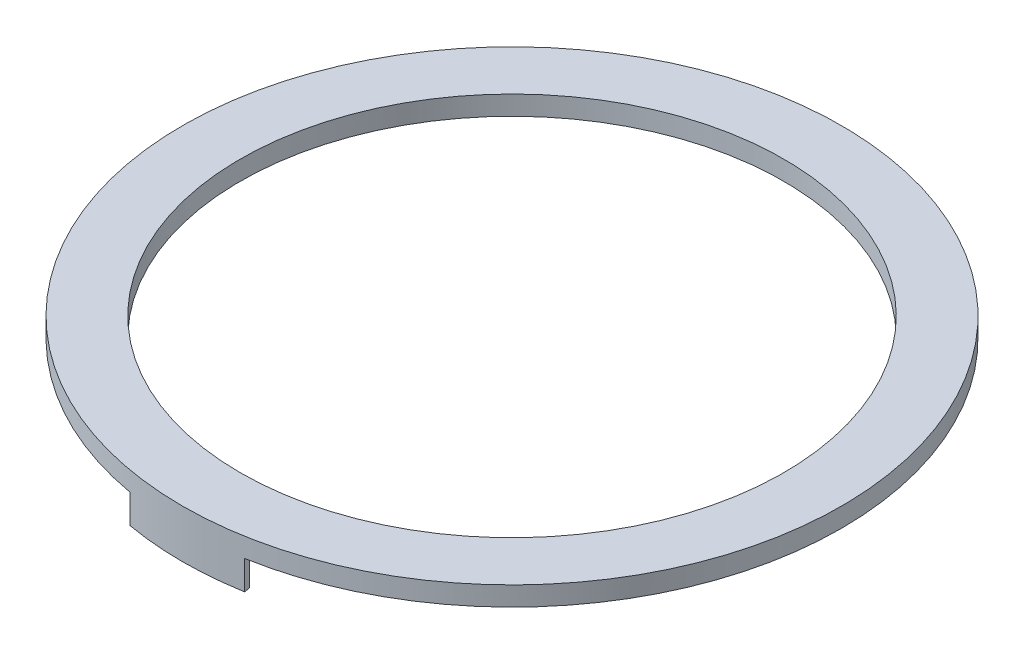
SolidWorks part; units mm, degrees
ref_plane "Front Plane" through (0, 0, 0) normal (0, 0, 1) x (1, 0, 0)
ref_plane "Top Plane" through (0, 0, 0) normal (0, 1, 0) x (1, 0, 0)
ref_plane "Right Plane" through (0, 0, 0) normal (1, 0, 0) x (0, 0, -1)
sketch "Sketch1" plane through (0, 0, 0) normal (0, 1, 0) x (1, 0, 0)
  circle A0 centre (0, 0) radius 171
extrude "Boss-Extrude1" add sketch "Sketch1" along normal blind 10 contours A0
sketch "Sketch2" plane through (0, 10, 0) normal (0, 1, 0) x (1, 0, 0)
  circle A0 centre (0, 0) radius 141
extrude "Cut-Extrude1" cut sketch "Sketch2" against normal through all contours A0
sketch "Sketch3" plane through (0, 0, 0) normal (0, -1, 0) x (1, 0, 0)
  line L0 (29.6938, 168.4021) -> (29.1729, 165.4477)
  line L1 (-29.7305, 168.3956) -> (-29.0797, 165.4641)
  arc A0 (-0.0373, 171) -> (29.6938, 168.4021) centre (0, 0) cw
  circle A1 centre (0, 0) radius 171 construction
  arc A2 (-0.0373, 171) -> (-29.7305, 168.3956) centre (0, 0) ccw
  arc A3 (0.0946, 168) -> (29.1729, 165.4477) centre (0, 0) cw
  arc A4 (0.0946, 168) -> (-29.0797, 165.4641) centre (0, 0) ccw
extrude "Boss-Extrude2" add sketch "Sketch3" along normal blind 15 contours A4 L1 A2 A0 L0 A3
sketch "Sketch4" plane through (0, 0, 0) normal (0, -1, 0) x (1, 0, 0)
  line L0 (29.7122, -168.3989) -> (29.1206, -165.4569)
  line L1 (-29.27, -165.4306) -> (-29.6755, -168.4054)
  arc A0 (0.0186, -171) -> (29.7122, -168.3989) centre (0, 0) ccw
  arc A1 (-29.7305, 168.3956) -> (29.6938, 168.4021) centre (0, 0) ccw construction
  arc A2 (0.0186, -171) -> (-29.6755, -168.4054) centre (0, 0) cw
  arc A3 (-0.0986, -168) -> (29.1206, -165.4569) centre (0, 0) ccw
  arc A4 (-0.0986, -168) -> (-29.27, -165.4306) centre (0, 0) cw
  dimension "D1" = 168
  dimension "D2" = 4.0668
extrude "Boss-Extrude3" add sketch "Sketch4" along normal blind 15 contours A4 L1 A2 A0 L0 A3
